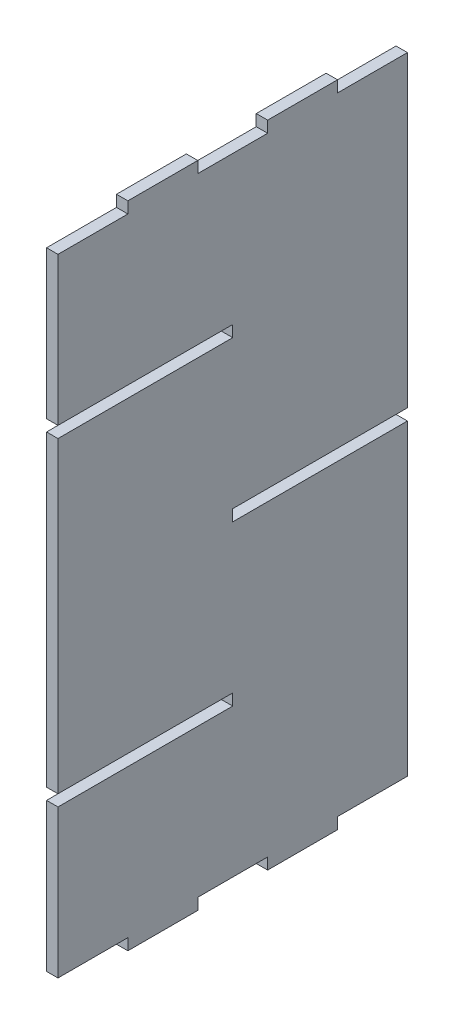
SolidWorks part; units mm, degrees
ref_plane "Piano frontale" through (0, 0, 0) normal (0, 0, 1) x (1, 0, 0)
ref_plane "Piano superiore" through (0, 0, 0) normal (0, 1, 0) x (1, 0, 0)
ref_plane "Piano destro" through (0, 0, 0) normal (1, 0, 0) x (0, 0, -1)
sketch "Schizzo1" plane through (0, 0, 0) normal (1, 0, 0) x (0, 0, -1)
  line L0 (-46, 43.5) -> (46, 43.5) construction
  line L1 (-46, -82.5) -> (46, -82.5) construction
  line L2 (-46, -82.5) -> (-46, -43.5)
  line L3 (-46, 82.5) -> (46, 82.5) construction
  line L5 (-46, -82.5) -> (46, 82.5) construction
  line L6 (-46, 82.5) -> (46, -82.5) construction
  line L7 (-46, 40.5) -> (46, 40.5) construction
  line L8 (0, 82.5) -> (0, -82.5) construction
  line L9 (-46, 0) -> (46, 0) construction
  line L10 (-46, 1.5) -> (46, 1.5) construction
  line L11 (-46, -1.5) -> (46, -1.5) construction
  line L12 (-46, -40.5) -> (46, -40.5) construction
  line L13 (-46, -43.5) -> (46, -43.5) construction
  line L14 (-46, -82.5) -> (46, -82.5) construction
  line L16 (-46, 40.5) -> (-46, 1.5) construction
  line L20 (-46, -43.5) -> (0, -43.5)
  line L21 (0, -43.5) -> (0, -40.5)
  line L22 (0, -40.5) -> (-46, -40.5)
  line L23 (46, -1.5) -> (0, -1.5)
  line L24 (0, -1.5) -> (0, 1.5)
  line L25 (0, 1.5) -> (46, 1.5)
  line L26 (-46, 40.5) -> (0, 40.5)
  line L27 (0, 40.5) -> (0, 43.5)
  line L28 (0, 43.5) -> (-46, 43.5)
  line L29 (-46, 43.5) -> (-46, 82.5)
  line L30 (46, 1.5) -> (46, 82.5)
  line L31 (-46, -40.5) -> (-46, 40.5)
  line L32 (46, -82.5) -> (46, -1.5)
  line L33 (-46, 82.5) -> (-27.6, 82.5)
  line L34 (-27.6, 82.5) -> (-27.6, 85.5)
  line L35 (-27.6, 85.5) -> (-9.2, 85.5)
  line L36 (-9.2, 85.5) -> (-9.2, 82.5)
  line L37 (-9.2, 82.5) -> (9.2, 82.5)
  line L38 (9.2, 82.5) -> (9.2, 85.5)
  line L39 (9.2, 85.5) -> (27.6, 85.5)
  line L40 (27.6, 85.5) -> (27.6, 82.5)
  line L41 (27.6, 82.5) -> (46, 82.5)
  line L42 (27.6, -82.5) -> (46, -82.5)
  line L43 (27.6, -85.5) -> (27.6, -82.5)
  line L44 (9.2, -85.5) -> (27.6, -85.5)
  line L45 (9.2, -82.5) -> (9.2, -85.5)
  line L46 (-9.2, -82.5) -> (9.2, -82.5)
  line L47 (-9.2, -85.5) -> (-9.2, -82.5)
  line L48 (-27.6, -85.5) -> (-9.2, -85.5)
  line L49 (-27.6, -82.5) -> (-27.6, -85.5)
  line L50 (-46, -82.5) -> (-27.6, -82.5)
  line L51 (-46, -85.5) -> (46, -85.5) construction
  point P0 (0, 0)
  dimension "D1" = 39
  dimension "D2" = 92
  dimension "D3" = 3
  dimension "D5" = 39
  dimension "D7" = 3
  dimension "D4" = 4
extrude "Estrusione-Estrusione1" add sketch "Schizzo1" along normal mid plane 3
